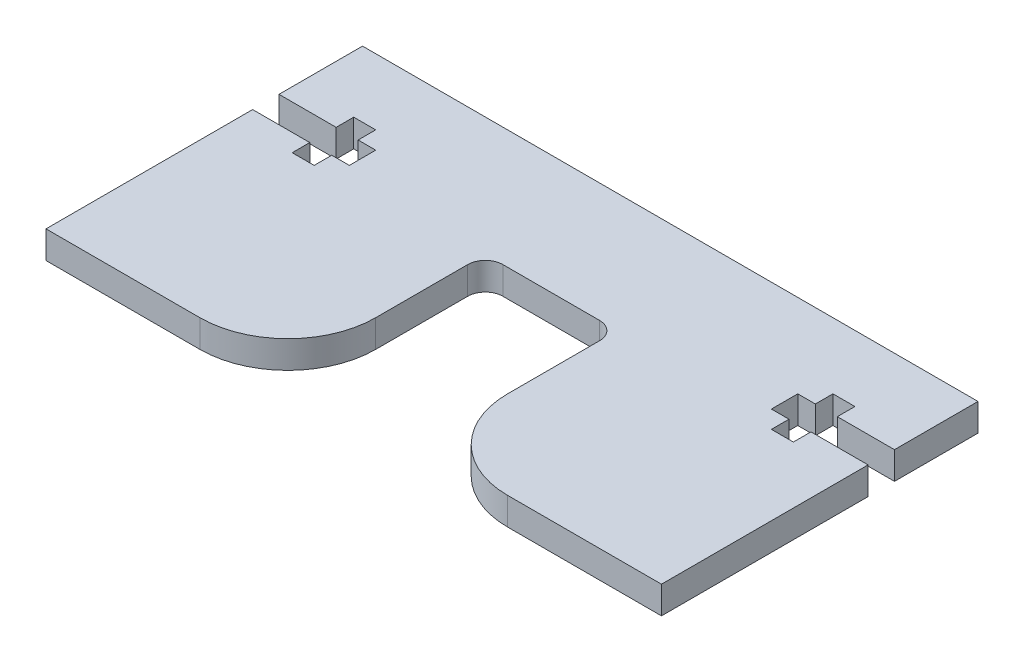
SolidWorks part; units mm, degrees
ref_plane "Front Plane" through (0, 0, 0) normal (0, 0, 1) x (1, 0, 0)
ref_plane "Top Plane" through (0, 0, 0) normal (0, 1, 0) x (1, 0, 0)
ref_plane "Right Plane" through (0, 0, 0) normal (1, 0, 0) x (0, 0, -1)
sketch "Sketch1" plane through (0, 0, 0) normal (0, 1, 0) x (1, 0, 0)
  line L0 (0, 25) -> (35, 25) construction
  line L1 (0, 36) -> (35, 36)
  line L2 (0, 36) -> (0, 0)
  line L3 (0, 0) -> (35, 0)
  line L4 (35, 36) -> (35, 26.5)
  line L5 (35, 26.5) -> (28.5, 26.5)
  line L6 (28.5, 26.5) -> (28.5, 28.5)
  line L7 (28.5, 28.5) -> (26, 28.5)
  line L8 (26, 28.5) -> (26, 26.5)
  line L9 (26, 26.5) -> (24, 26.5)
  line L10 (24, 26.5) -> (24, 23.5)
  line L11 (24, 23.5) -> (26, 23.5)
  line L12 (26, 23.5) -> (26, 21.5)
  line L13 (26, 21.5) -> (28.5, 21.5)
  line L14 (28.5, 21.5) -> (28.5, 23.5)
  line L15 (28.5, 23.5) -> (35, 23.5)
  line L16 (35, 23.5) -> (35, 0)
  point P17 (24, 25)
  dimension "D1" = 35
  dimension "D2" = 2.5
  dimension "D3" = 9
  dimension "D4" = 2
  dimension "D5" = 3
  dimension "D6" = 7.5
  dimension "D7" = 7
  dimension "D8" = 25
extrude "Boss-Extrude1" add sketch "Sketch1" along normal mid plane 3.125
mirror "Mirror1" about plane through (0, 0, 0) normal (1, 0, 0) of "Boss-Extrude1"
sketch "Sketch2" plane through (0, -1.5625, 0) normal (0, -1, 0) x (1, 0, 0)
  line L0 (-35, 0) -> (35, 0) construction
  line L1 (-7.5, 0) -> (7.5, 0)
  line L2 (-7.5, 0) -> (-7.5, -22.4625)
  line L3 (-7.5, -22.4625) -> (7.5, -22.4625)
  line L4 (7.5, 0) -> (7.5, -22.4625)
  line L5 (-7.5, 0) -> (7.5, -22.4625) construction
  line L6 (-7.5, -22.4625) -> (7.5, 0) construction
  line L7 (0, -11.2313) -> (0, 0) construction
  line L8 (-30, -9.9625) -> (30, -9.9625) construction
  point P4 (0, -11.2313)
  dimension "D1" = 15
  dimension "D2" = 12.5
extrude "Cut-Extrude1" cut sketch "Sketch2" against normal through all
fillet "Fillet1" radius 10 2 edges at (-7.5, 0, 0) (7.5, 0, 0)
fillet "Fillet2" radius 2 2 edges at (7.5, 0, -22.4625) (-7.5, 0, -22.4625)
